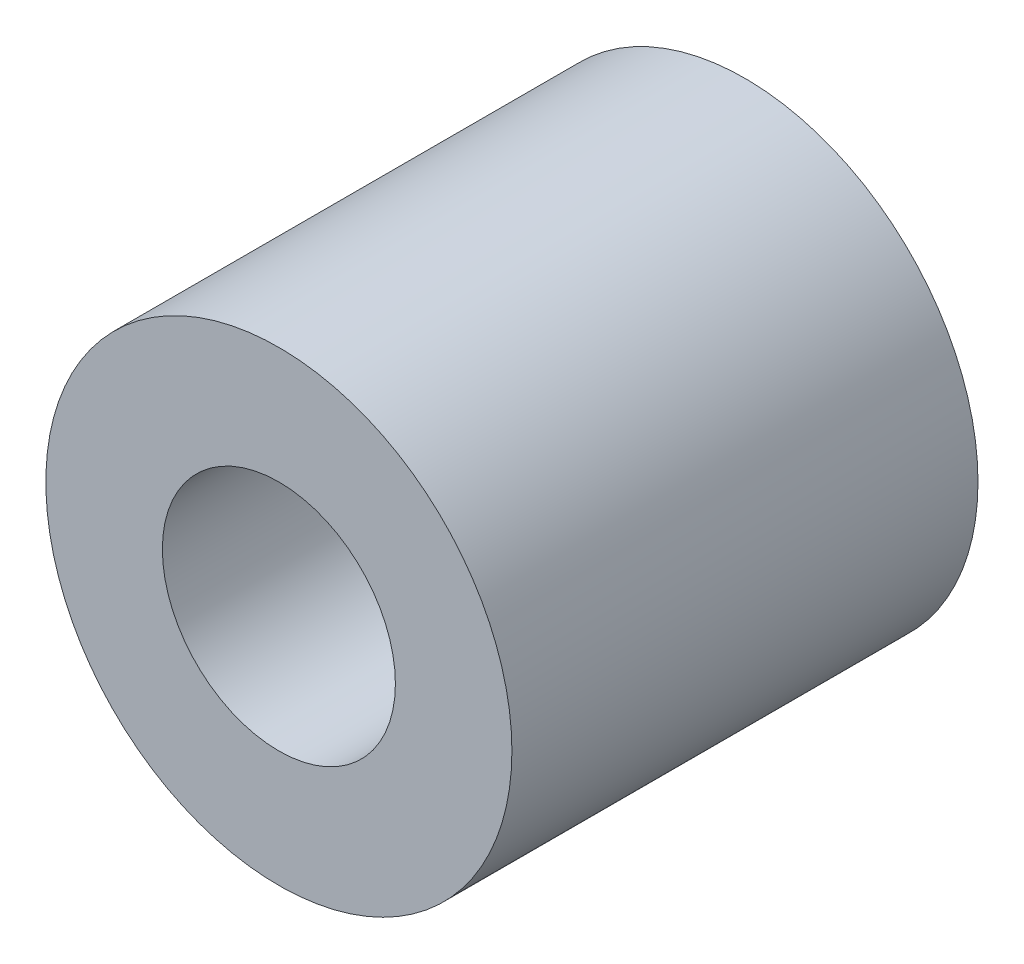
SolidWorks part; units mm, degrees
ref_plane "Front Plane" through (0, 0, 0) normal (0, 0, 1) x (1, 0, 0)
ref_plane "Top Plane" through (0, 0, 0) normal (0, 1, 0) x (1, 0, 0)
ref_plane "Right Plane" through (0, 0, 0) normal (1, 0, 0) x (0, 0, -1)
sketch "Sketch1" plane through (0, 0, 0) normal (0, 0, 1) x (1, 0, 0)
  circle A0 centre (0, 0) radius 3.175
  circle A1 centre (0, 0) radius 1.5875
  dimension "D1" = 6.35
  dimension "ID" = 3.175
extrude "Extrude1" add sketch "Sketch1" along normal mid plane 6.35
sketch "Sketch2" plane through (0, 0, 0) normal (1, 0, 0) x (0, 0, -1)
  line L0 (-3.175, -1.5875) -> (3.175, -1.5875) construction
  line L3 (3.175, 1.5875) -> (-3.175, 1.5875) construction
  line L5 (-3.175, -1.5875) -> (3.175, -1.5875)
  line L6 (3.175, 1.5875) -> (-3.175, 1.5875)
sketch "Sketch4" plane through (0, 0, 3.175) normal (0, 0, 1) x (1, 0, 0)
  line L0 (0, 0) -> (-1.1225, 1.1225)
  line L1 (0, -3.4925) -> (0, 3.4925) construction
  circle A0 centre (0, 0) radius 1.5875 construction
  dimension "D1" = 45
